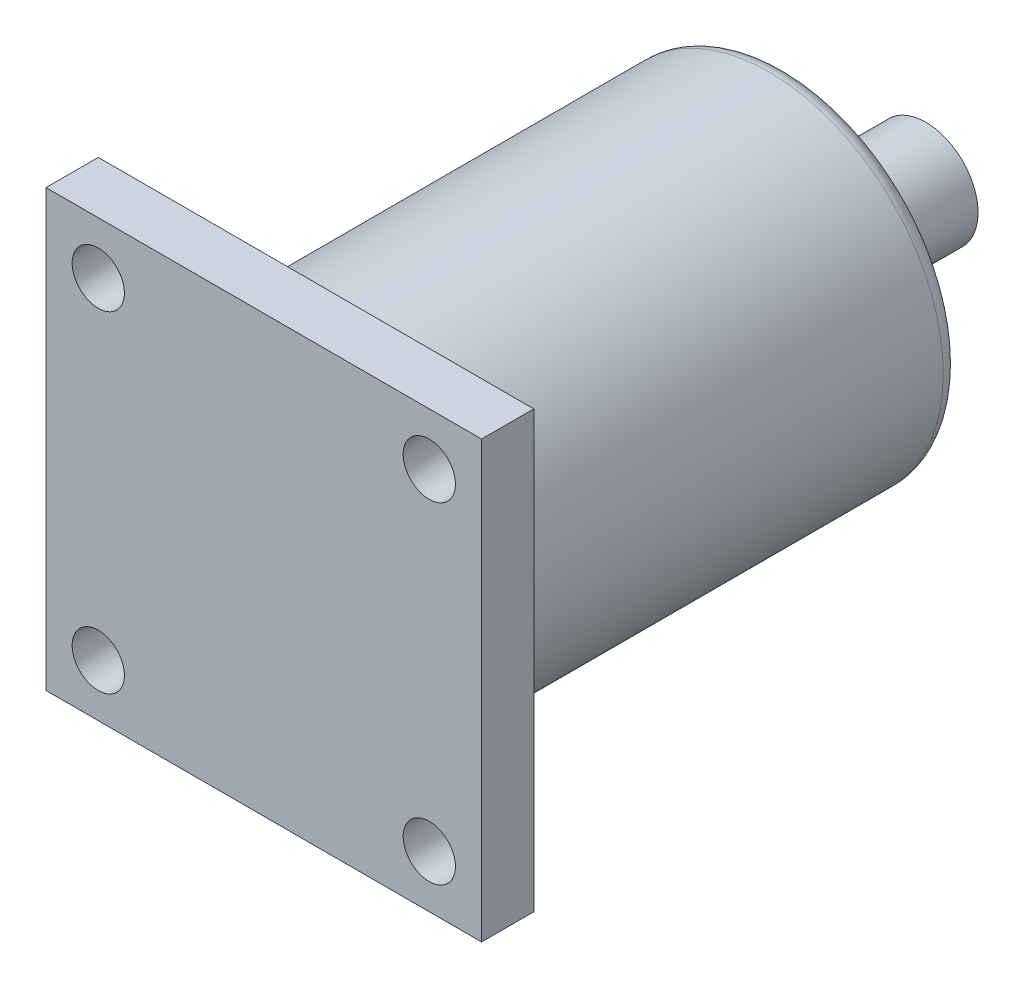
SolidWorks part; units mm, degrees
ref_plane "前视基准面" through (0, 0, 0) normal (0, 0, 1) x (1, 0, 0)
ref_plane "上视基准面" through (0, 0, 0) normal (0, 1, 0) x (1, 0, 0)
ref_plane "右视基准面" through (0, 0, 0) normal (1, 0, 0) x (0, 0, -1)
sketch "草图2" plane through (0, 0, 0) normal (0, 0, 1) x (1, 0, 0)
  line L1 (0, 0) -> (25, 0)
  line L2 (0, 0) -> (0, -25)
  line L3 (0, -25) -> (25, -25)
  line L4 (25, 0) -> (25, -25)
  dimension "D1" = 25
  dimension "D2" = 25
extrude "凸台-拉伸1" add sketch "草图2" along normal blind 3
sketch "草图3" plane through (0, 0, 0) normal (0, 0, -1) x (-1, 0, 0)
  line L0 (-12.5, 0) -> (-12.5, -16.674) construction
  line L1 (-25, 0) -> (0, 0) construction
  line L2 (-25, -12.5) -> (0, -12.5) construction
  line L3 (-25, -25) -> (-25, 0) construction
  line L4 (0, 0) -> (0, -25) construction
  circle A0 centre (-22, -3) radius 1.5
  circle A1 centre (-3, -3) radius 1.5
  circle A2 centre (-3, -22) radius 1.5
  circle A3 centre (-22, -22) radius 1.5
  dimension "D3" = 3
  dimension "D1" = 3
  dimension "D2" = 3
extrude "切除-拉伸2" cut sketch "草图3" against normal through all
sketch "草图4" plane through (0, 0, 3) normal (0, 0, 1) x (1, 0, 0)
  line L0 (0, 0) -> (25, -25) construction
  line L7 (19, -19) -> (6, -6) construction
  circle A0 centre (12.5, -12.5) radius 10
  point P4 (12.5, -12.5)
  dimension "D1" = 20
extrude "凸台-拉伸2" add sketch "草图4" against normal blind 27 from surface at -3 starting at face at (23.5, -22, 0)
sketch "草图5" plane through (0, 0, -27) normal (0, 0, -1) x (-1, 0, 0)
  line L0 (-21.2215, -17.3924) -> (-3.7785, -7.6076) construction
  circle A3 centre (-12.5, -12.5) radius 10 construction
  circle A4 centre (-12.5, -12.5) radius 3
  dimension "D1" = 6
extrude "凸台-拉伸3" add sketch "草图5" along normal blind 8
fillet "圆角3" radius 1 2 edges at (22.5, -12.5, -27) (22.5, -12.5, 0)
